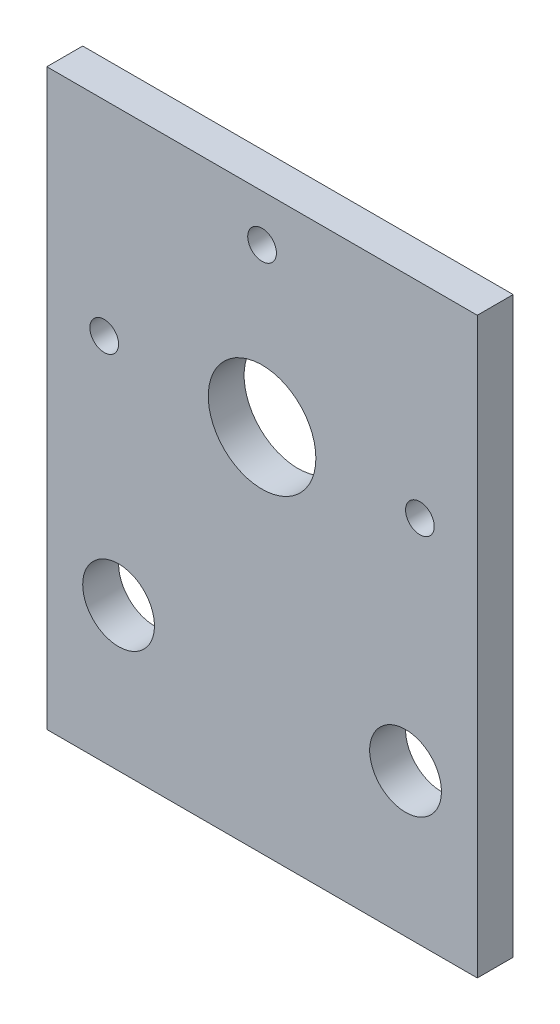
SolidWorks part; units mm, degrees
ref_plane "Front Plane" through (0, 0, 0) normal (0, 0, 1) x (1, 0, 0)
ref_plane "Top Plane" through (0, 0, 0) normal (0, 1, 0) x (1, 0, 0)
ref_plane "Right Plane" through (0, 0, 0) normal (1, 0, 0) x (0, 0, -1)
other "Center of Mass"
sketch "Sketch1" plane through (0, 0, 0) normal (0, 0, 1) x (1, 0, 0)
  line L0 (-30, -20) -> (30, -20) construction
  line L1 (-30, 40) -> (30, 40)
  line L2 (-30, 40) -> (-30, -40)
  line L3 (-30, -40) -> (30, -40)
  line L4 (30, 40) -> (30, -40)
  line L5 (-30, 40) -> (30, -40) construction
  line L6 (-30, -40) -> (30, 40) construction
  line L7 (0, 11.5) -> (0, -47.6893) construction
  line L8 (0, 11.5) -> (0, 33.5) construction
  circle A0 centre (0, 11.5) radius 7.5
  circle A1 centre (20, -20) radius 5
  circle A4 centre (0, 33.5) radius 2
  circle A6 centre (-22, 11.5) radius 2
  circle A7 centre (-20, -20) radius 5
  circle A8 centre (22, 11.5) radius 2
  point P0 (0, 0)
  dimension "D4" = 15
  dimension "D6" = 10
  dimension "D7" = 22
  dimension "D8" = 4
  dimension "D1" = 80
  dimension "D2" = 60
  dimension "D3" = 20
  dimension "D5" = 51.5
  dimension "D9" = 22
  dimension "D10" = 20
extrude "Boss-Extrude1" add sketch "Sketch1" along normal blind 5
